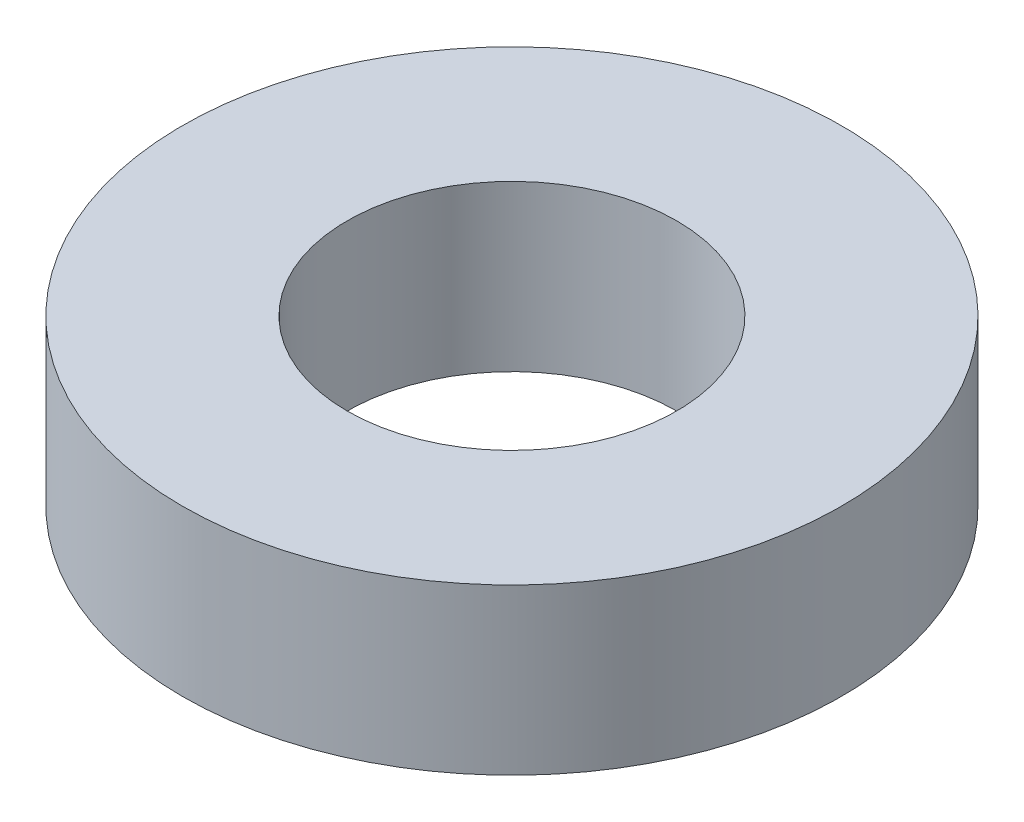
SolidWorks part; units mm, degrees
ref_plane "前视基准面" through (0, 0, 0) normal (0, 0, 1) x (1, 0, 0)
ref_plane "上视基准面" through (0, 0, 0) normal (0, 1, 0) x (1, 0, 0)
ref_plane "右视基准面" through (0, 0, 0) normal (1, 0, 0) x (0, 0, -1)
sketch "草图1" plane through (0, 0, 0) normal (0, 1, 0) x (1, 0, 0)
  circle A0 centre (0, 0) radius 4
  circle A1 centre (0, 0) radius 8
extrude "凸台-拉伸1" add sketch "草图1" along normal blind 4
